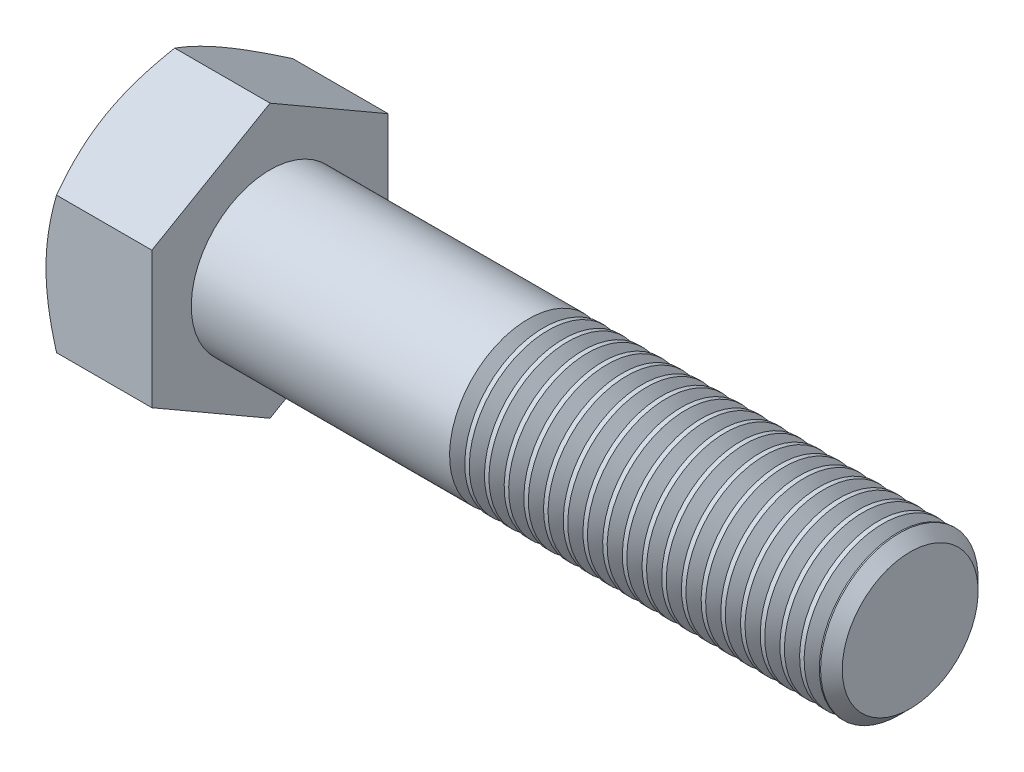
SolidWorks part; units mm, degrees
extrude "BaseHead" add sketch "Sketch1" along normal blind 10.75
sketch "Sketch1" plane through (0, 0, 0) normal (1, 0, 0) x (0, 0, -1)
  line L0 (12, 6.9282) -> (12, -6.9282)
  line L1 (-12, 6.9282) -> (-12, -6.9282)
  line L2 (12, -6.9282) -> (0, -13.8564)
  line L3 (0, -13.8564) -> (-12, -6.9282)
  line L4 (12, 6.9282) -> (0, 13.8564)
  line L5 (0, 13.8564) -> (-12, 6.9282)
  dimension "Width_flats" = 24
  dimension "D2" = 120
  dimension "D3" = 12
  dimension "D4" = 12
  dimension "D5" = 12
ref_plane "Plane1" through (0, 0, 0) normal (0, 0, 1) x (1, 0, 0)
ref_plane "Plane2" through (0, 0, 0) normal (0, 1, 0) x (1, 0, 0)
ref_plane "Plane3" through (0, 0, 0) normal (1, 0, 0) x (0, 0, -1)
sketch "BodySke" plane through (0, 0, 0) normal (0, 0, 1) x (1, 0, 0)
  line L0 (0, 6.9282) -> (0, -6.9282) construction
  line L1 (0, 0) -> (75.75, 0)
  line L2 (0, 0) -> (0, 8)
  line L3 (0, 8) -> (74.6485, 8)
  line L4 (75.75, 0) -> (75.75, 6.8985)
  line L5 (10.75, 13.8564) -> (10.75, 6.9282) construction
  line L6 (75.75, 6.8985) -> (74.6485, 8)
  line L7 (0, 0) -> (96.52, 0) construction
  line L8 (75.75, -6.8985) -> (74.6485, -8) construction
  line L9 (0, -8) -> (74.6485, -8) construction
  line L10 (12.75, 15.24) -> (12.75, -1.27) construction
  line L11 (37.75, 15.24) -> (37.75, -1.27) construction
  line L12 (10.75, 6.9282) -> (10.75, -6.9282) construction
  dimension "Diameter" = 16
  dimension "Advance" = 2
revolve "BaseBody" add sketch "BodySke"
cosmetic thread "ThreadCosmetic" [suppressed]
fillet "HeadFillet" [suppressed] radius 0.6
sketch "Sketch3" plane through (0, 0, 0) normal (0, 0, 1) x (1, 0, 0)
  line L0 (0, 12) -> (3.9585, 18.8564)
  line L1 (0, 13.8564) -> (0, 6.9282) construction
  line L2 (3.9585, 18.8564) -> (3.9585, 23.8564)
  line L3 (3.9585, 23.8564) -> (-10, 23.8564)
  line L4 (-10, 23.8564) -> (-10, 12)
  line L5 (-10, 12) -> (0, 12)
  line L6 (0, 0) -> (99.06, 0) construction
  line L7 (10.75, 13.8564) -> (0, 13.8564) construction
  dimension "D1" = 12
  dimension "D2" = 5
  dimension "D3" = 10
  dimension "D4" = 5
  dimension "Head_ch_ang" = 30
revolve "HeadChamfer" cut sketch "Sketch3" angle 360 about L6
sketch "ThdSchSke" plane through (0, 0, 0) normal (0, 0, 1) x (1, 0, 0)
  line L0 (37.75, -6.8985) -> (36.9787, -8)
  line L1 (37.75, -6.8985) -> (38.5213, -8)
  line L2 (38.5213, -8) -> (38.5213, -10)
  line L3 (-3.175, 0) -> (5.1513, 0) construction
  line L5 (38.5213, -10) -> (36.9787, -10)
  line L6 (36.9787, -10) -> (36.9787, -8)
  dimension "Thread_minor" = 13.797
  dimension "Diameter" = 16
  dimension "Start" = 37.75
revolve "ThreadSchematic" cut sketch "ThdSchSke" angle 360 about L3
pattern_linear "ThdSchPat" count 19 spacing 2 along (1, 0, 0) of "ThreadSchematic"
equation "\"D3@Sketch1\" = \"Width_flats@Sketch1\" / 2"
equation "\"D4@Sketch1\" = \"D3@Sketch1\""
equation "\"D5@Sketch1\" = \"D4@Sketch1\""
equation "\"Thread_minor@ThreadCosmetic\" = \"Minor_dia@BodySke\""
equation "\"D1@Sketch3\" = \"Width_flats@Sketch1\" / 2"
equation "' \"D1@Sketch4\" = \"Width_flats@Sketch1\""
equation "\"Thread_length@ThreadCosmetic\" = ((sgn( (\"Length@BodySke\" - \"Advance@BodySke\" ) - \"Thread_nom@BodySke\" )-1)*( (\"Length@BodySke\" - \"Advance@BodySke\" ) - \"Thread_nom@BodySke\" ))/-2+ \"Thread_nom@BodySke\""
equation "\"Thread_minor@ThdSchSke\" = \"Minor_dia@BodySke\""
equation "\"Diameter@ThdSchSke\" = \"Diameter@BodySke\""
equation "\"Overcut@ThdSchSke\" = \"Diameter@BodySke\" * 1.25"
equation "\"Start@ThdSchSke\" = \"Head_ht@BaseHead\" + \"Length@BodySke\" - \"Thread_length@ThreadCosmetic\"  '---Non-countersunk---"
equation "\"Num_threads@ThdSchPat\" = int( \"Thread_length@ThreadCosmetic\" / \"Advance@BodySke\" + 0.999 )  + 1"
equation "\"Advance@ThdSchPat\" = \"Thread_length@ThreadCosmetic\" /  (\"Num_threads@ThdSchPat\" - 1) 'relax it"
equation "\"Num_threads@ThdSchPat\" = \"Num_threads@ThdSchPat\" - sgn( \"Num_threads@ThdSchPat\" - 1) '---chamfered tips only---"
